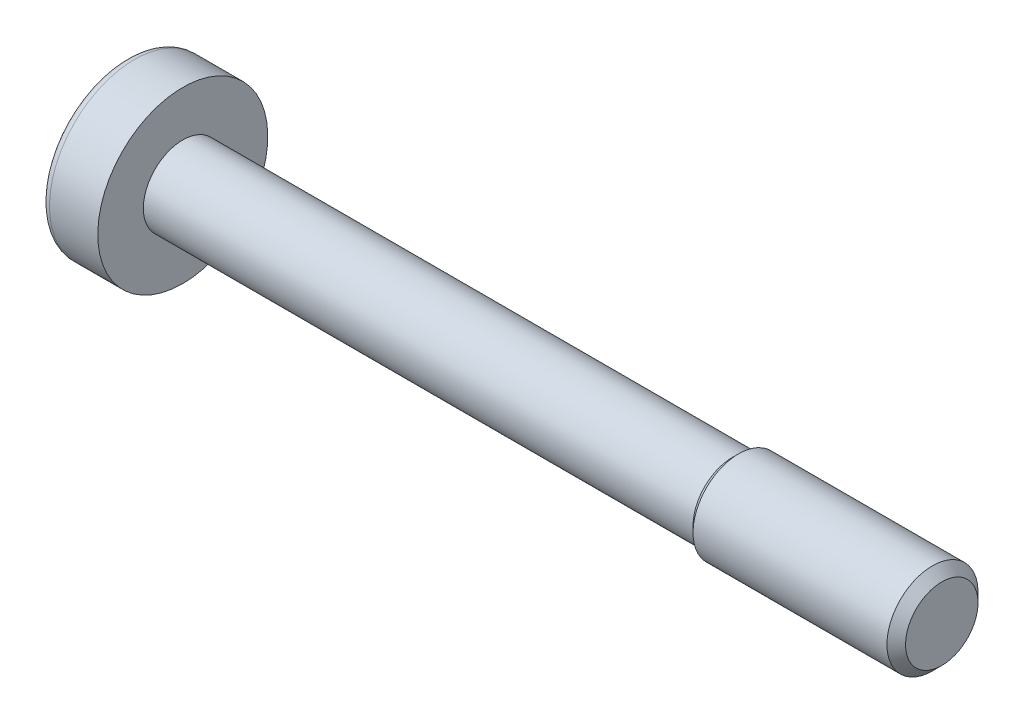
SolidWorks part; units mm, degrees
ref_plane "Front Plane" through (0, 0, 0) normal (0, 0, 1) x (1, 0, 0)
ref_plane "Top Plane" through (0, 0, 0) normal (0, 1, 0) x (1, 0, 0)
ref_plane "Right Plane" through (0, 0, 0) normal (1, 0, 0) x (0, 0, -1)
ref_plane "Plane1" through (0, 0, 0) normal (0, 0, 1) x (1, 0, 0)
sketch "Sketch1" plane through (0, 0, 0) normal (0, 0, 1) x (1, 0, 0)
  line L0 (-1.5917, 0) -> (-2.4, 1.4)
  line L1 (-1.591, 2.8) -> (0, 2.8)
  line L2 (0, 2.8) -> (0, 1.3)
  line L3 (0, 1.3) -> (18.1065, 1.3)
  line L4 (18.1065, 1.3) -> (18.3065, 1.5)
  line L5 (18.3065, 1.5) -> (24.6935, 1.5)
  line L6 (24.6935, 1.5) -> (25, 1.1935)
  line L7 (25, 1.1935) -> (25, 0)
  line L8 (25, 0) -> (-1.5917, 0)
  line L9 (25, 0) -> (-1.5917, 0) construction
  arc A0 (-2.4, 1.4) -> (-1.8277, 2.6695) centre (2.4, 0) cw
  arc A1 (-1.8277, 2.6695) -> (-1.591, 2.8) centre (-1.591, 2.52) cw
revolve "Revolve1" add sketch "Sketch1" angle 360 about L9
cosmetic thread "Cosmetic Thread1" parameters "D1"=6.8935, "D2"=2.387
ref_plane "Plane2" through (-2.4, 0, 0) normal (1, 0, 0) x (0, 0, -1)
sketch "Sketch2" plane through (-2.4, 0, 0) normal (1, 0, 0) x (0, 0, -1)
  arc A0 (-1.1621, -0.3564) -> (-0.8897, -0.8282) centre (-0.9699, -0.56) ccw
  arc A1 (-0.8897, -0.8282) -> (-0.2724, -1.1846) centre (-0.7492, -1.2977) cw
  arc A2 (-0.2724, -1.1846) -> (0.2724, -1.1846) centre (0, -1.12) ccw
  arc A3 (0.2724, -1.1846) -> (0.8897, -0.8282) centre (0.7492, -1.2977) cw
  arc A4 (0.8897, -0.8282) -> (1.1621, -0.3564) centre (0.9699, -0.56) ccw
  arc A5 (1.1621, -0.3564) -> (1.1621, 0.3564) centre (1.4984, 0) cw
  arc A6 (1.1621, 0.3564) -> (0.8897, 0.8282) centre (0.9699, 0.56) ccw
  arc A7 (0.8897, 0.8282) -> (0.2724, 1.1846) centre (0.7492, 1.2977) cw
  arc A8 (0.2724, 1.1846) -> (-0.2724, 1.1846) centre (0, 1.12) ccw
  arc A9 (-0.2724, 1.1846) -> (-0.8897, 0.8282) centre (-0.7492, 1.2977) cw
  arc A10 (-0.8897, 0.8282) -> (-1.1621, 0.3564) centre (-0.9699, 0.56) ccw
  arc A11 (-1.1621, 0.3564) -> (-1.1621, -0.3564) centre (-1.4984, 0) cw
extrude "Cut-Extrude1" cut sketch "Sketch2" along normal blind 2.16
ref_plane "Plane3" through (-2.4, 0, 0) normal (1, 0, 0) x (0, 0, -1)
sketch "Sketch3" plane through (-2.4, 0, 0) normal (1, 0, 0) x (0, 0, -1)
  line L0 (-2.4, 0.44) -> (-2.4, -0.44)
  line L1 (-2.4, -0.44) -> (2.4, -0.44)
  line L2 (2.4, -0.44) -> (2.4, 0.44)
  line L3 (2.4, 0.44) -> (-2.4, 0.44)
extrude "Cut-Extrude2" cut sketch "Sketch3" along normal blind 2.16
